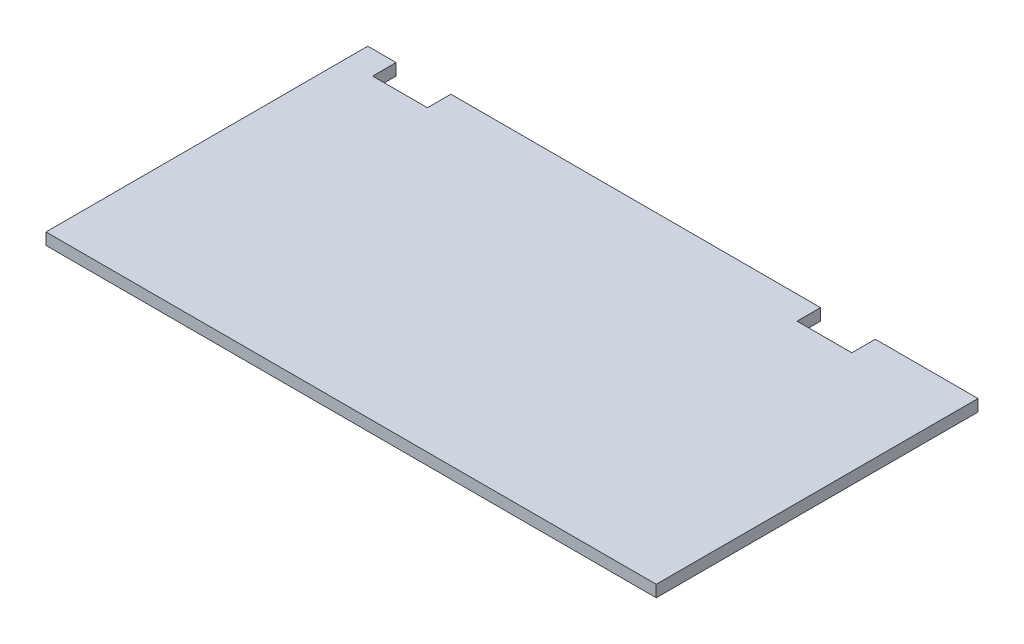
SolidWorks part; units mm, degrees
ref_plane "Front Plane" through (0, 0, 0) normal (0, 0, 1) x (1, 0, 0)
ref_plane "Top Plane" through (0, 0, 0) normal (0, 1, 0) x (1, 0, 0)
ref_plane "Right Plane" through (0, 0, 0) normal (1, 0, 0) x (0, 0, -1)
sketch "Sketch1" plane through (0, 0, 0) normal (0, 1, 0) x (1, 0, 0)
  line L1 (0, 0) -> (990.6, 0)
  line L2 (0, 0) -> (0, 522.2875)
  line L3 (0, 522.2875) -> (990.6, 522.2875)
  line L4 (990.6, 0) -> (990.6, 522.2875)
  dimension "D1" = 522.2875
  dimension "D2" = 990.6
extrude "Boss-Extrude1" add sketch "Sketch1" along normal blind 19.05
sketch "Sketch2" plane through (0, 19.05, 0) normal (0, 1, 0) x (1, 0, 0)
  line L1 (823.9125, 484.1875) -> (735.0125, 484.1875)
  line L2 (823.9125, 484.1875) -> (823.9125, 522.2875)
  line L3 (823.9125, 522.2875) -> (735.0125, 522.2875)
  line L4 (735.0125, 484.1875) -> (735.0125, 522.2875)
  line L6 (46.0375, 522.2875) -> (134.9375, 522.2875)
  line L7 (46.0375, 522.2875) -> (46.0375, 484.1875)
  line L8 (46.0375, 484.1875) -> (134.9375, 484.1875)
  line L9 (134.9375, 522.2875) -> (134.9375, 484.1875)
  line L10 (0, 522.2875) -> (0, 0) construction
  line L12 (990.6, 522.2875) -> (0, 522.2875) construction
  dimension "D1" = 46.0375
  dimension "D2" = 88.9
  dimension "D3" = 735.0125
  dimension "D4" = 88.9
  dimension "D5" = 38.1
extrude "Cut-Extrude1" cut sketch "Sketch2" against normal through all
